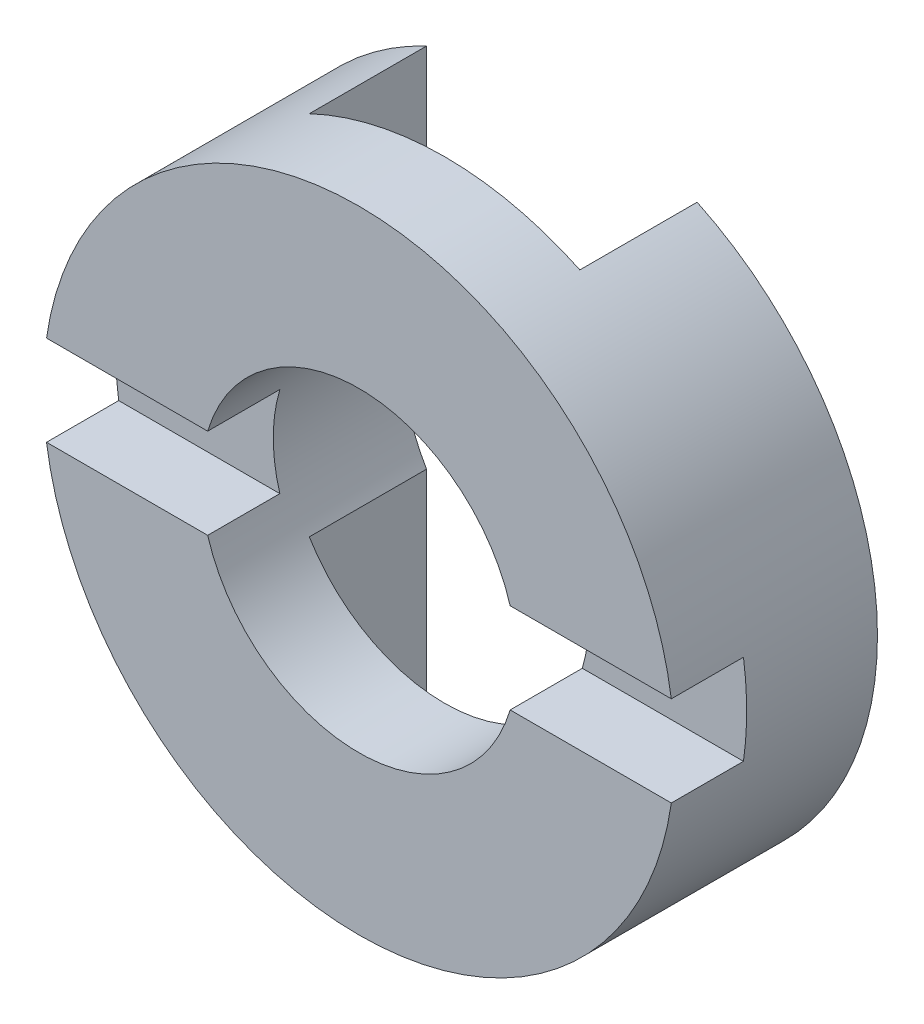
SolidWorks part; units mm, degrees
material "2024-T3"
ref_plane "Спереди" through (0, 0, 0) normal (0, 0, 1) x (1, 0, 0)
ref_plane "Сверху" through (0, 0, 0) normal (0, 1, 0) x (1, 0, 0)
ref_plane "Справа" through (0, 0, 0) normal (1, 0, 0) x (0, 0, -1)
sketch "Эскиз1" plane through (0, 0, 0) normal (0, 0, 1) x (1, 0, 0)
  line L0 (1, 3.5) -> (-1, -3.5) construction
  line L1 (-3, -3.5) -> (-3, 3.5)
  line L2 (3, -3.5) -> (3, 3.5)
  line L3 (-1, 5.5) -> (1, 5.5)
  line L4 (-1, -5.5) -> (1, -5.5)
  line L5 (1, -3.5) -> (-1, 3.5) construction
  arc A0 (-6.8374, -1.5) -> (6.8374, -1.5) centre (0, 0) cw
  arc A1 (-3, -3.5) -> (-1, -5.5) centre (-1, -3.5) ccw
  arc A2 (1, 5.5) -> (3, 3.5) centre (1, 3.5) cw
  arc A3 (-6.8374, -1.5) -> (6.8374, -1.5) centre (0, 0) ccw
  arc A4 (-1, 5.5) -> (-3, 3.5) centre (-1, 3.5) ccw
  arc A5 (3, -3.5) -> (1, -5.5) centre (1, -3.5) cw
  circle A6 centre (0, 0) radius 3.5
  point P5 (0, 0)
  dimension "D1" = 6
  dimension "D2" = 7
  dimension "D3" = 11
  dimension "D4" = 2
  dimension "D5" = 7
extrude "Бобышка-Вытянуть1" add sketch "Эскиз1" along normal blind 4.5 contours A0 A3 A6 L1 A4 L3 A2 L2 A5 L4 A1 | A6 L2 A2 L3 A4 L1 | A6 L1 A1 L4 A5 L2
sketch "Эскиз2" plane through (0, 0, 0) normal (0, 1, 0) x (1, 0, 0)
  line L0 (7, 0) -> (-7, 0) construction
  line L1 (-3, 0) -> (3, 0)
  line L2 (-3, 0) -> (-3, -2.6)
  line L3 (-3, -2.6) -> (3, -2.6)
  line L4 (3, 0) -> (3, -2.6)
  dimension "D1" = 6
  dimension "D2" = 2.6
extrude "Вырез-Вытянуть1" cut sketch "Эскиз2" against normal through all and the other way through all
sketch "Эскиз3" plane through (0, 0, 0) normal (1, 0, 0) x (0, 0, -1)
  line L0 (-4.5, 7) -> (-4.5, -7) construction
  line L1 (-4.5, 1) -> (-2.9, 1)
  line L2 (-4.5, 1) -> (-4.5, -1)
  line L3 (-4.5, -1) -> (-2.9, -1)
  line L4 (-2.9, 1) -> (-2.9, -1)
  line L5 (-4.5, 0) -> (0, 0) construction
  dimension "D1" = 1.6
  dimension "D2" = 2
extrude "Вырез-Вытянуть2" cut sketch "Эскиз3" against normal through all and the other way through all
